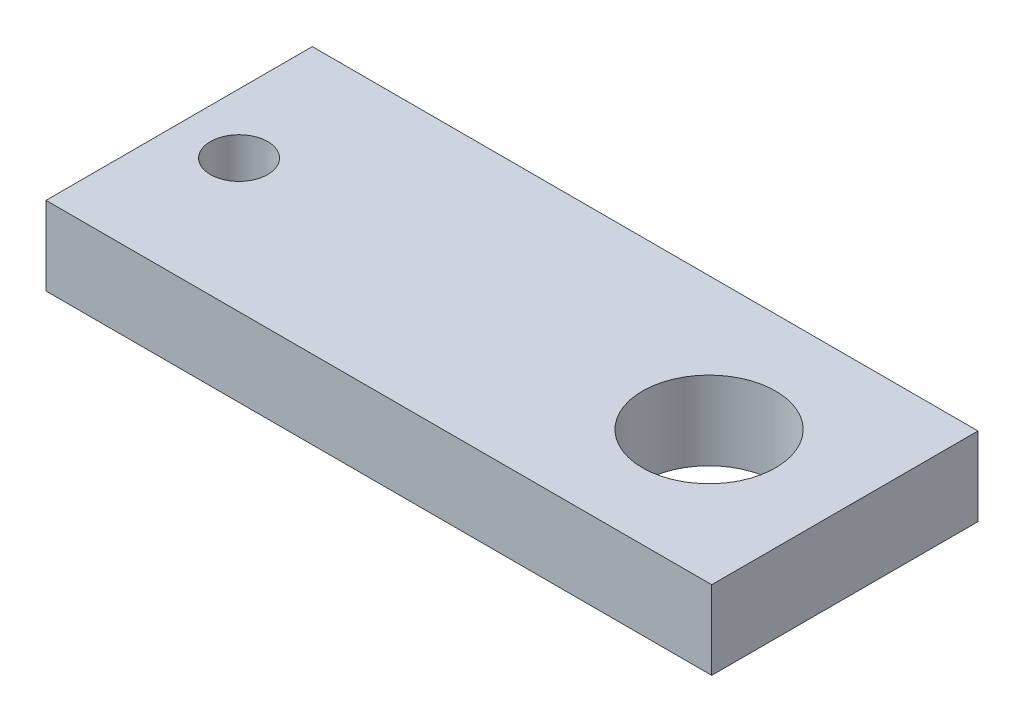
SolidWorks part; units mm, degrees
ref_plane "Front Plane" through (0, 0, 0) normal (0, 0, 1) x (1, 0, 0)
ref_plane "Top Plane" through (0, 0, 0) normal (0, 1, 0) x (1, 0, 0)
ref_plane "Right Plane" through (0, 0, 0) normal (1, 0, 0) x (0, 0, -1)
sketch "Sketch1" plane through (0, 0, 0) normal (0, 1, 0) x (1, 0, 0)
  line L0 (0, 0) -> (-25, 0) construction
  line L1 (-25, -10) -> (25, -10)
  line L2 (-25, -10) -> (-25, 10)
  line L3 (-25, 10) -> (25, 10)
  line L4 (25, -10) -> (25, 10)
  line L5 (-25, -10) -> (25, 10) construction
  line L6 (-25, 10) -> (25, -10) construction
  circle A0 centre (14.8, 0) radius 5
  circle A1 centre (-20.5, 0) radius 2.15
  point P0 (0, 0)
  dimension "D3" = 10
  dimension "D5" = 4.3
  dimension "D1" = 50
  dimension "D2" = 20
  dimension "D4" = 10.2
  dimension "D6" = 4.5
extrude "Boss-Extrude1" add sketch "Sketch1" along normal blind 5.9
equation "\"e\" = 5.9"
equation "\"D1@Boss-Extrude1\"=\"e\""
